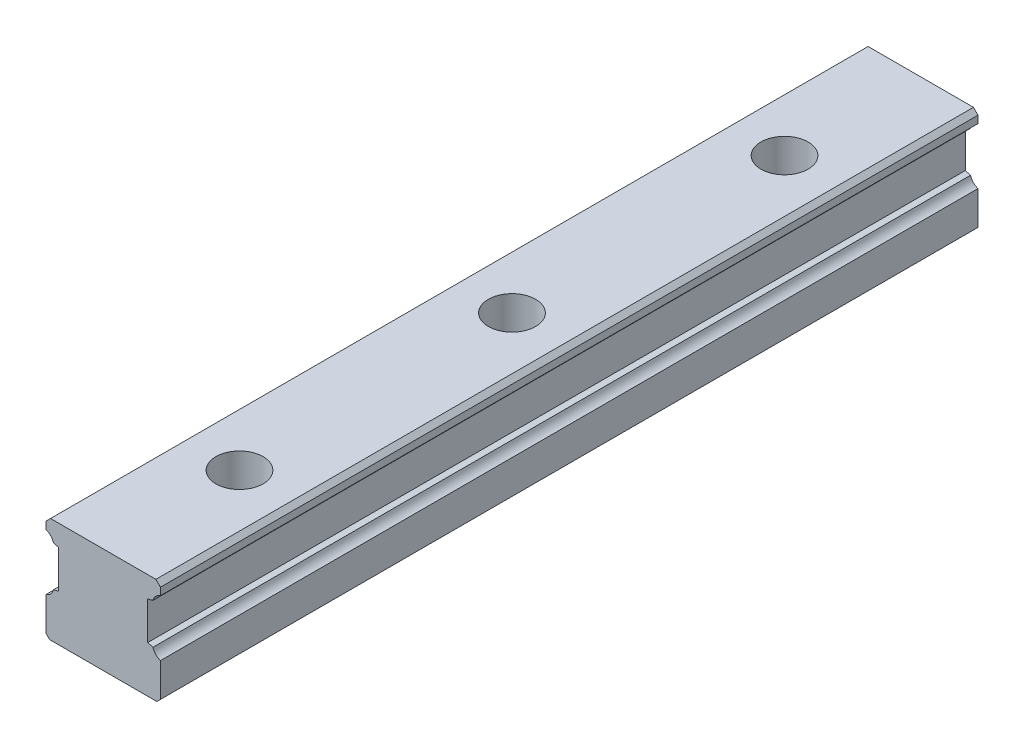
SolidWorks part; units mm, degrees
ref_plane "Plano frontal" through (0, 0, 0) normal (0, 0, 1) x (1, 0, 0)
ref_plane "Plano superior" through (0, 0, 0) normal (0, 1, 0) x (1, 0, 0)
ref_plane "Plano direito" through (0, 0, 0) normal (1, 0, 0) x (0, 0, -1)
sketch "Esboço1" plane through (0, 0, 0) normal (0, 0, 1) x (1, 0, 0)
  line L0 (-31.5, 20.5273) -> (-31.5, 0)
  line L1 (-31.5, 0) -> (31.5, 0)
  line L2 (31.5, 0) -> (31.5, 20.5273)
  line L3 (27.3973, 24.8216) -> (24.5, 25.5979)
  line L4 (24.5, 25.5979) -> (24.5, 46.3977)
  line L5 (24.5, 46.3977) -> (27.3971, 47.1739)
  line L6 (31.5, 51.4749) -> (31.5, 58)
  line L7 (31.5, 58) -> (-31.5, 58)
  line L8 (-31.5, 58) -> (-31.5, 51.4749)
  line L9 (-27.3978, 47.1758) -> (-24.5, 46.3997)
  line L10 (-24.5, 46.3997) -> (-24.5, 25.597)
  line L11 (-24.5, 25.597) -> (-27.3979, 24.8234)
  arc A0 (-27.3979, 24.8234) -> (-31.5, 20.5273) centre (-33.3777, 26.4267) cw
  arc A1 (31.5, 20.5273) -> (27.3973, 24.8216) centre (33.3765, 26.4271) cw
  arc A2 (27.3971, 47.1739) -> (31.5, 51.4749) centre (33.3782, 45.5757) cw
  arc A3 (-31.5, 51.4749) -> (-27.3978, 47.1758) centre (-33.3784, 45.5757) cw
extrude "Ressalto-extrusão1" add sketch "Esboço1" along normal blind 450
hole_wizard "Rebaixo para parafuso de cabeça sextavada de M161" positions "Esboço3" profile "Esboço2" counterbore size "M16" standard "Ansi Metric"
sketch "Esboço3" plane through (0, 58, 0) normal (0, 1, 0) x (1, 0, 0)
  point P0 (0, -75)
  point P1 (0, -1425)
  point P2 (0, -1275)
  point P3 (0, -1125)
  point P4 (0, -975)
  point P5 (0, -825)
  point P6 (0, -675)
  point P7 (0, -525)
  point P8 (0, -375)
  point P9 (0, -225)
sketch "Esboço2" plane through (0, 58, 75) normal (1, 0, 0) x (0, 0, 1)
  line L0 (0, 0) -> (0, 58)
  line L1 (0, 58) -> (9, 58)
  line L3 (9, 58) -> (9, 25)
  line L4 (9, 25) -> (13, 25)
  line L5 (13, 25) -> (13, 0)
  line L7 (13, 0) -> (0, 0)
  line L11 (0, -6.35) -> (0, 107.95) construction
  dimension "Thru Hole Dia." = 18
  dimension "Thru Hole Depth" = 58
  dimension "C'Bore Dia." = 26
  dimension "C'Bore Depth" = 25
chamfer "Chanfro1" distance 2.5003 angle 45 1 edges at (-31.5, 58, 225)
chamfer "Chanfro2" distance 2.5003 angle 45.002 1 edges at (31.5, 58, 225)
chamfer "Chanfro3" distance 2 angle 45 2 edges at (31.5, 0, 225) (-31.5, 0, 225)
